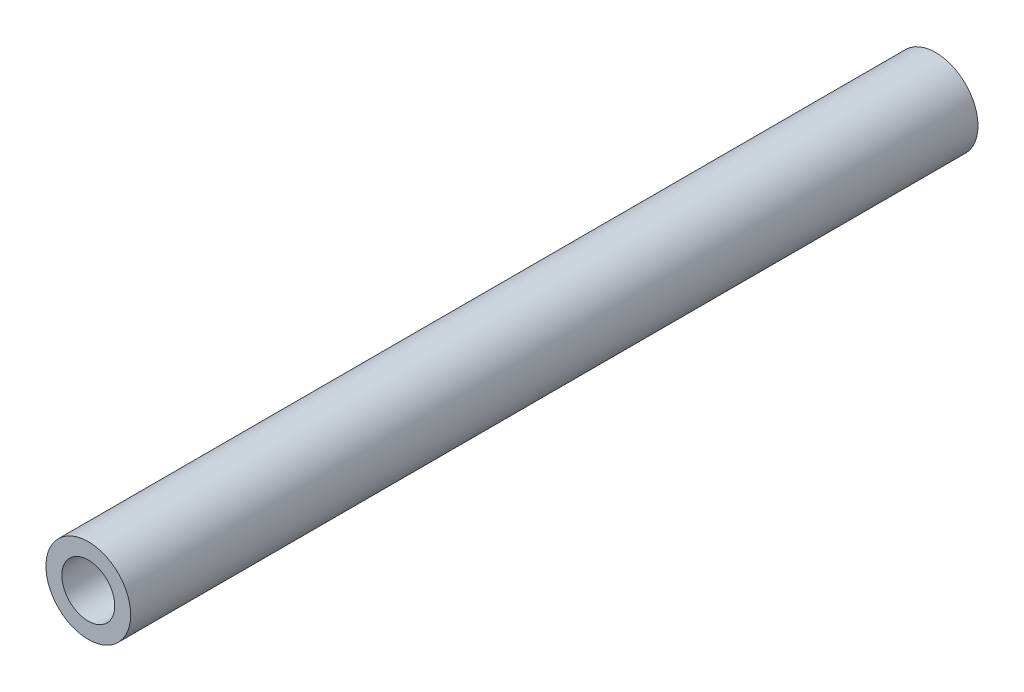
SolidWorks part; units mm, degrees
ref_plane "前视基准面" through (0, 0, 0) normal (0, 0, 1) x (1, 0, 0)
ref_plane "上视基准面" through (0, 0, 0) normal (0, 1, 0) x (1, 0, 0)
ref_plane "右视基准面" through (0, 0, 0) normal (1, 0, 0) x (0, 0, -1)
sketch "草图1" plane through (0, 0, 0) normal (0, 0, 1) x (1, 0, 0)
  circle A0 centre (0, 0) radius 1.6
  circle A1 centre (0, 0) radius 1
  dimension "D1" = 3.2
  dimension "D2" = 2
extrude "凸台-拉伸1" add sketch "草图1" along normal blind 32
